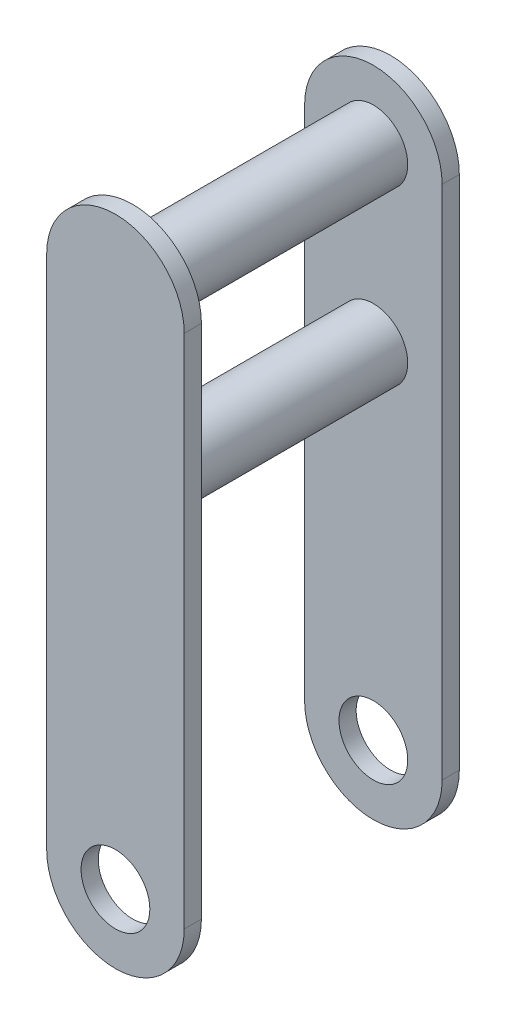
SolidWorks part; units mm, degrees
material "AISI 4340 Steel, normalized"
ref_plane "Front Plane" through (0, 0, 0) normal (0, 0, 1) x (1, 0, 0)
ref_plane "Top Plane" through (0, 0, 0) normal (0, 1, 0) x (1, 0, 0)
ref_plane "Right Plane" through (0, 0, 0) normal (1, 0, 0) x (0, 0, -1)
sketch "Sketch1" plane through (0, 0, 0) normal (0, 0, 1) x (1, 0, 0)
  line L0 (0, 0) -> (0, 300) construction
  line L1 (-40, 0) -> (-40, 300)
  line L2 (40, 0) -> (40, 300)
  arc A1 (-40, 0) -> (40, 0) centre (0, 0) ccw
  arc A2 (40, 300) -> (-40, 300) centre (0, 300) ccw
  circle A3 centre (0, 0) radius 20
  circle A4 centre (0, 300) radius 20 construction
  circle A5 centre (0, 200) radius 20 construction
  point P3 (0, 150)
  dimension "D2" = 40
  dimension "D3" = 20
  dimension "D1" = 300
  dimension "D4" = 100
extrude "Boss-Extrude1" add sketch "Sketch1" along normal mid plane 10 from offset 75
sketch "Sketch2" plane through (0, 0, 70) normal (0, 0, -1) x (-1, 0, 0)
  circle A0 centre (0, 300) radius 20 construction
  circle A1 centre (0, 200) radius 20 construction
  circle A2 centre (0, 300) radius 20
  circle A3 centre (0, 200) radius 20
extrude "Boss-Extrude2" add sketch "Sketch2" along normal blind 140
mirror "Mirror2" about plane through (0, 0, 0) normal (0, 0, 1) of "Boss-Extrude1"
